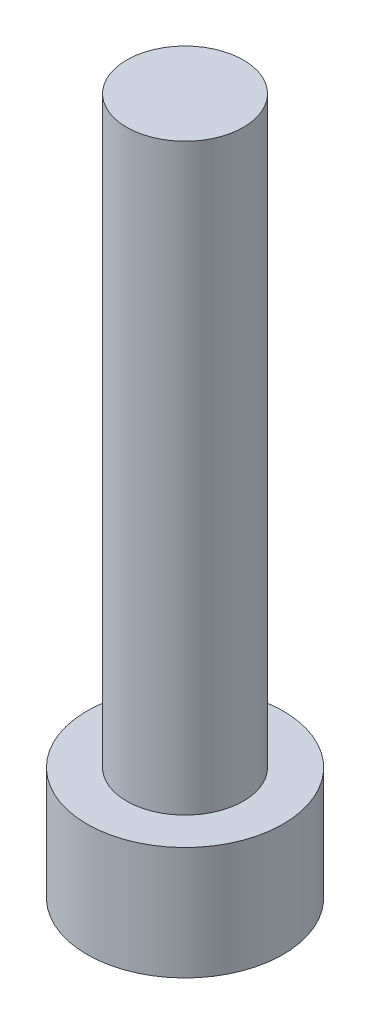
SolidWorks part; units mm, degrees
ref_plane "前视基准面" through (0, 0, 0) normal (0, 0, 1) x (1, 0, 0)
ref_plane "上视基准面" through (0, 0, 0) normal (0, 1, 0) x (1, 0, 0)
ref_plane "右视基准面" through (0, 0, 0) normal (1, 0, 0) x (0, 0, -1)
sketch "草图1" plane through (0, 0, 0) normal (0, 1, 0) x (1, 0, 0)
  circle A0 centre (0, 0) radius 4.2
extrude "凸台-拉伸1" add sketch "草图1" along normal blind 4.84
sketch "草图2" plane through (0, 4.84, 0) normal (0, 1, 0) x (1, 0, 0)
  circle A0 centre (0, 0) radius 2.5
extrude "凸台-拉伸2" add sketch "草图2" along normal blind 25
sketch "草图3" plane through (0, 0, 0) normal (0, -1, 0) x (1, 0, 0)
  line L1 (2.3, 0) -> (1.15, 1.9919)
  line L2 (1.15, 1.9919) -> (-1.15, 1.9919)
  line L3 (-1.15, 1.9919) -> (-2.3, 0)
  line L4 (-2.3, 0) -> (-1.15, -1.9919)
  line L5 (-1.15, -1.9919) -> (1.15, -1.9919)
  line L6 (1.15, -1.9919) -> (2.3, 0)
  circle A0 centre (0, 0) radius 1.9919 construction
extrude "切除-拉伸1" cut sketch "草图3" against normal blind 3.4
